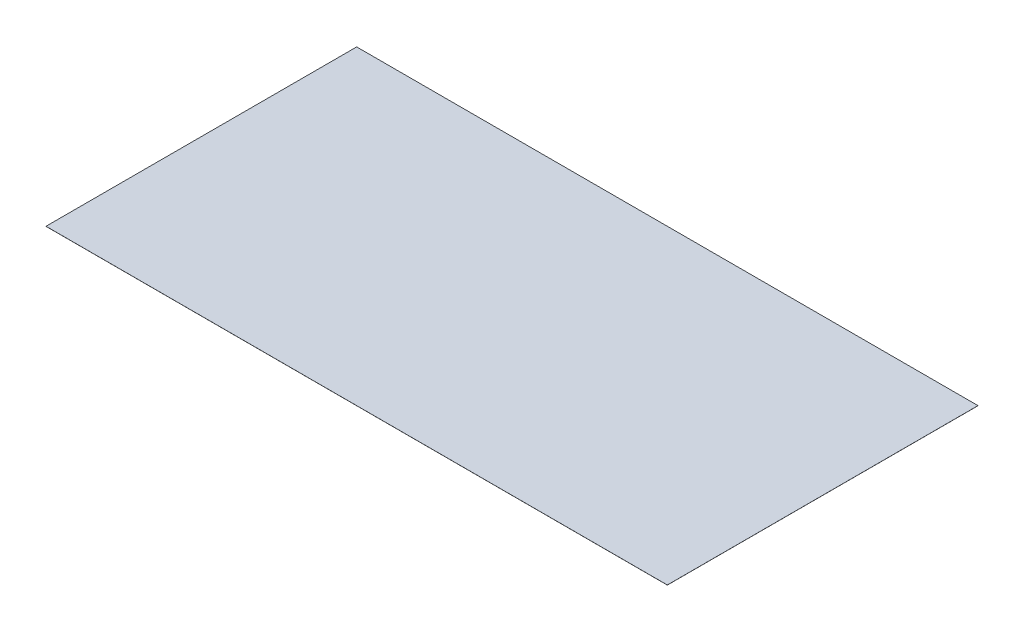
SolidWorks part; units mm, degrees
ref_plane "Front" through (0, 0, 0) normal (0, 0, 1) x (1, 0, 0)
ref_plane "Top" through (0, 0, 0) normal (0, 1, 0) x (1, 0, 0)
ref_plane "Right" through (0, 0, 0) normal (1, 0, 0) x (0, 0, -1)
sketch "Sketch1" plane through (0, 0, 0) normal (0, 1, 0) x (1, 0, 0)
  line L1 (0, 0) -> (16459.2, 0)
  line L2 (0, 0) -> (0, 8229.6)
  line L3 (0, 8229.6) -> (16459.2, 8229.6)
  line L4 (16459.2, 0) -> (16459.2, 8229.6)
  line L5 (0, 0) -> (16459.2, 8229.6) construction
  line L6 (0, 8229.6) -> (16459.2, 0) construction
  point P4 (8229.6, 4114.8)
  dimension "D1" = 8229.6
  dimension "D2" = 16459.2
extrude "Boss-Extrude1" add sketch "Sketch1" along normal blind 2.54
